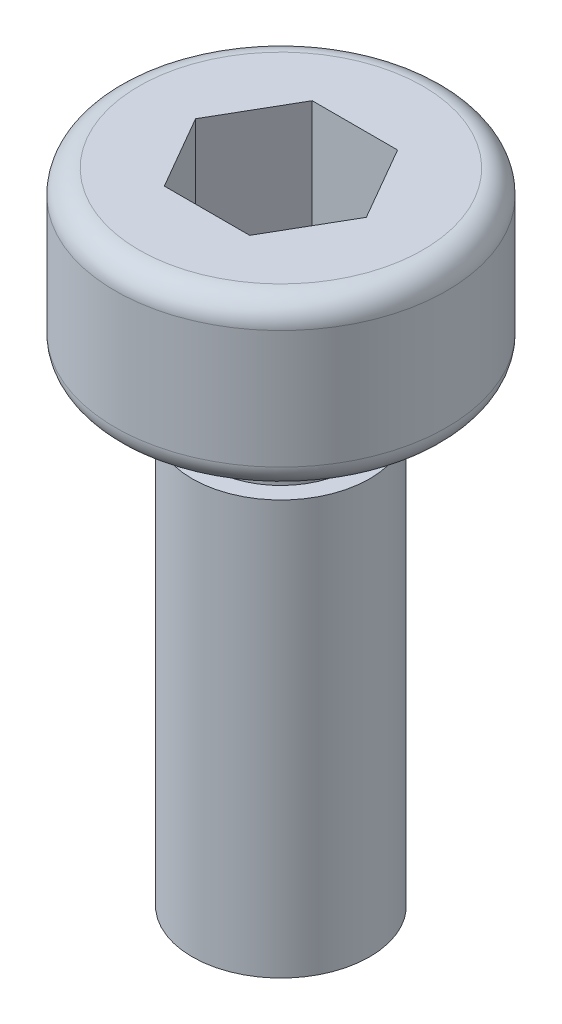
SolidWorks part; units mm, degrees
material "AISI 304"
ref_plane "前视基准面" through (0, 0, 0) normal (0, 0, 1) x (1, 0, 0)
ref_plane "上视基准面" through (0, 0, 0) normal (0, 1, 0) x (1, 0, 0)
ref_plane "右视基准面" through (0, 0, 0) normal (1, 0, 0) x (0, 0, -1)
sketch "草图1" plane through (0, 0, 0) normal (0, 0, 1) x (1, 0, 0)
  line L0 (0, 0) -> (0, 10.8) construction
  line L1 (0, 10.8) -> (-2.4, 10.8)
  line L2 (-2.8, 10.4) -> (-2.8, 8.4)
  line L3 (-2.4, 8) -> (-1.2, 8)
  line L4 (-1.2, 8) -> (-1.2, 7)
  line L5 (-1.2, 7) -> (-1.5, 7)
  line L6 (-1.5, 7) -> (-1.5, 0)
  line L7 (-1.5, 0) -> (0, 0)
  line L8 (0, 0) -> (0, 10.8)
  arc A0 (-2.8, 8.4) -> (-2.4, 8) centre (-2.4, 8.4) ccw
  arc A1 (-2.4, 10.8) -> (-2.8, 10.4) centre (-2.4, 10.4) ccw
  point P11 (-2.8, 8)
  point P14 (-2.8, 10.8)
  dimension "D7" = 0.4
  dimension "D1" = 8
  dimension "D2" = 2.8
  dimension "D3" = 5.6
  dimension "D4" = 3
  dimension "D5" = 1
  dimension "D6" = 1.2
revolve "旋转1" add sketch "草图1" angle 360 about L0
cosmetic thread "装饰螺纹线1"
sketch "草图2" plane through (0, 10.8, 0) normal (0, 1, 0) x (1, 0, 0)
  line L1 (-0.7217, 1.25) -> (-1.4434, 0)
  line L2 (-1.4434, 0) -> (-0.7217, -1.25)
  line L3 (-0.7217, -1.25) -> (0.7217, -1.25)
  line L4 (0.7217, -1.25) -> (1.4434, 0)
  line L5 (1.4434, 0) -> (0.7217, 1.25)
  line L6 (0.7217, 1.25) -> (-0.7217, 1.25)
  circle A0 centre (0, 0) radius 1.25 construction
  dimension "D1" = 2.5
extrude "切除-拉伸1" cut sketch "草图2" against normal blind 2
